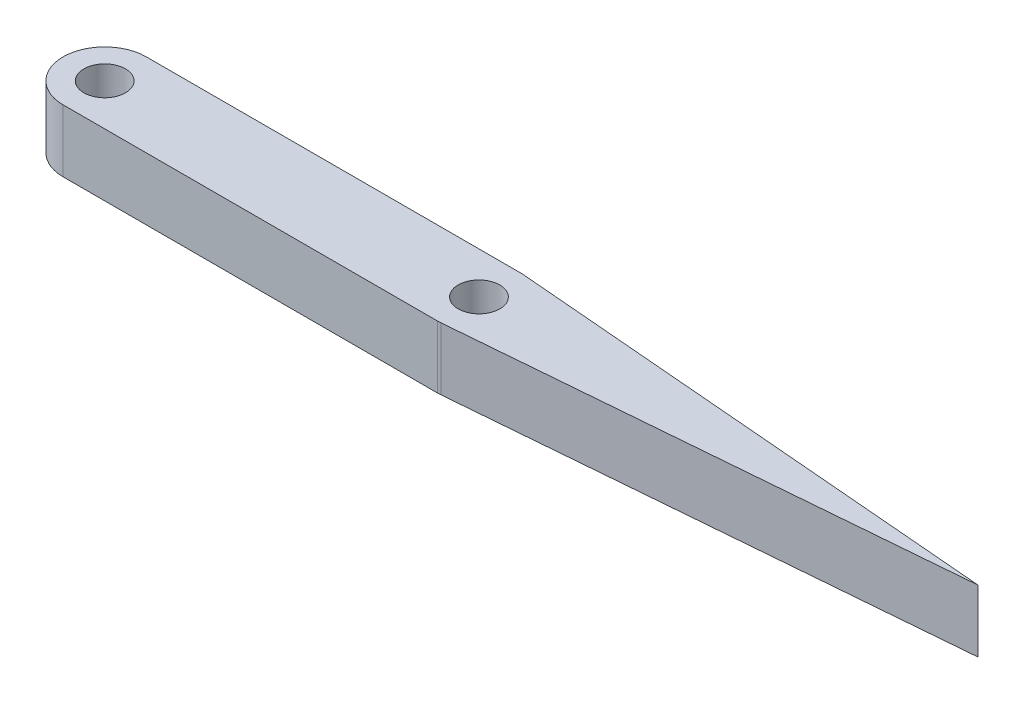
SolidWorks part; units mm, degrees
ref_plane "前视基准面" through (0, 0, 0) normal (0, 0, 1) x (1, 0, 0)
ref_plane "上视基准面" through (0, 0, 0) normal (0, 1, 0) x (1, 0, 0)
ref_plane "右视基准面" through (0, 0, 0) normal (1, 0, 0) x (0, 0, -1)
sketch "草图1" plane through (0, 0, 0) normal (0, 1, 0) x (1, 0, 0)
  line L0 (-17.5382, 0) -> (65.5869, 0) construction
  line L1 (0, 2) -> (18, 2)
  line L2 (18, -2) -> (0, -2)
  line L3 (18.1667, 1.993) -> (42, 0)
  line L5 (18.1667, -1.993) -> (42, 0)
  arc A0 (0, 2) -> (0, -2) centre (0, 0) ccw
  circle A1 centre (0, 0) radius 1
  arc A2 (18, -2) -> (18.1667, -1.993) centre (18, 0) ccw
  circle A3 centre (18, 0) radius 1
  arc A5 (18.1667, 1.993) -> (18, 2) centre (18, 0) ccw
  point P7 (0, 0)
  point P13 (41.9515, -1.5258)
  point P15 (41.9785, 0)
  point P17 (0, 0)
  point P18 (42, 0)
  dimension "D1" = 4
  dimension "D2" = 2
  dimension "D3" = 4
  dimension "D4" = 2
  dimension "D6" = 24
  dimension "D5" = 18
extrude "凸台-拉伸1" add sketch "草图1" along normal blind 3
